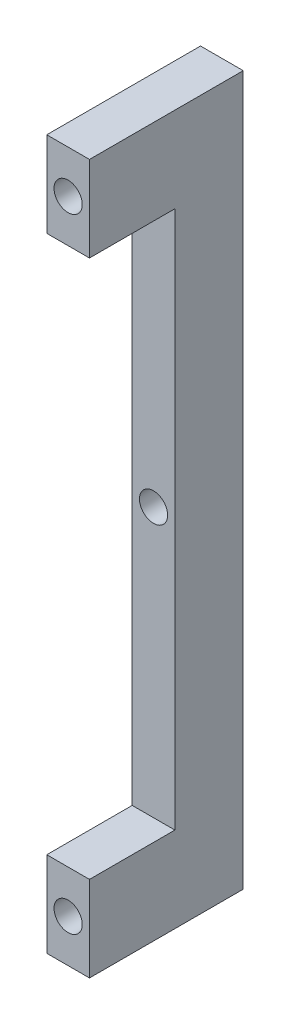
SolidWorks part; units mm, degrees
ref_plane "Plan de face" through (0, 0, 0) normal (0, 0, 1) x (1, 0, 0)
ref_plane "Plan de dessus" through (0, 0, 0) normal (0, 1, 0) x (1, 0, 0)
ref_plane "Plan de droite" through (0, 0, 0) normal (1, 0, 0) x (0, 0, -1)
sketch "Esquisse1" plane through (0, 0, 0) normal (0, 0, 1) x (1, 0, 0)
  line L0 (0, 0) -> (0, 73) construction
  line L2 (-2.5, 78) -> (2.5, 78)
  line L3 (-2.5, 78) -> (-2.5, -5)
  line L4 (-2.5, -5) -> (2.5, -5)
  line L5 (2.5, 78) -> (2.5, -5)
  point P0 (0, 0)
  point P1 (0, 73)
  point P4 (0, 36.5)
  dimension "D1" = 73
  dimension "D2" = 36.5
  dimension "D3" = 36.5
  dimension "D4" = 5
  dimension "D5" = 5
  dimension "D6" = 83
  dimension "D7" = 2.5
  dimension "D8" = 2.5
  dimension "D9" = 5
extrude "Boss.-Extru.1" add sketch "Esquisse1" against normal blind 18
hole_wizard "Trou taraudé M4" positions "Esquisse3" profile "Esquisse2" tap size "M4" standard "ISO" end condition through all
sketch "Esquisse3" plane through (0, 0, 0) normal (0, 0, 1) x (1, 0, 0)
  point P0 (0, 0)
  point P3 (0, 36.5)
  point P6 (0, 73)
sketch "Esquisse2" plane through (0, 0, 0) normal (1, 0, 0) x (0, -1, 0)
  line L0 (0, 0) -> (0, 18)
  line L1 (0, 18) -> (1.65, 18)
  line L2 (1.65, 18) -> (1.65, 0)
  line L5 (1.65, 0) -> (0, 0)
  line L11 (0, -6.35) -> (0, 107.95) construction
  dimension "Diamètre du trou pour taraudage jusqu'au prochain" = 3.3
  dimension "Profondeur du trou pour taraudage jusqu'au prochain" = 18
cosmetic thread "Filetage de perçage1" parameters "D2"=4
cosmetic thread "Filetage de perçage2" parameters "D2"=4
cosmetic thread "Filetage de perçage3" parameters "D2"=4
sketch "Esquisse4" plane through (0, 0, 0) normal (0, 0, 1) x (1, 0, 0)
  line L0 (-2.5, 78) -> (-2.5, -5) construction
  line L1 (-2.5, 68) -> (2.5, 68)
  line L2 (-2.5, 68) -> (-2.5, 5)
  line L3 (-2.5, 5) -> (2.5, 5)
  line L4 (2.5, 68) -> (2.5, 5)
  line L5 (2.5, -5) -> (2.5, 78) construction
  line L6 (-2.5, -5) -> (2.5, -5) construction
  line L7 (-2.5, 78) -> (2.5, 78) construction
  dimension "D1" = 63
  dimension "D3" = 10
  dimension "D4" = 10
extrude "Enlèv. mat.-Extru.1" cut sketch "Esquisse4" against normal blind 10
